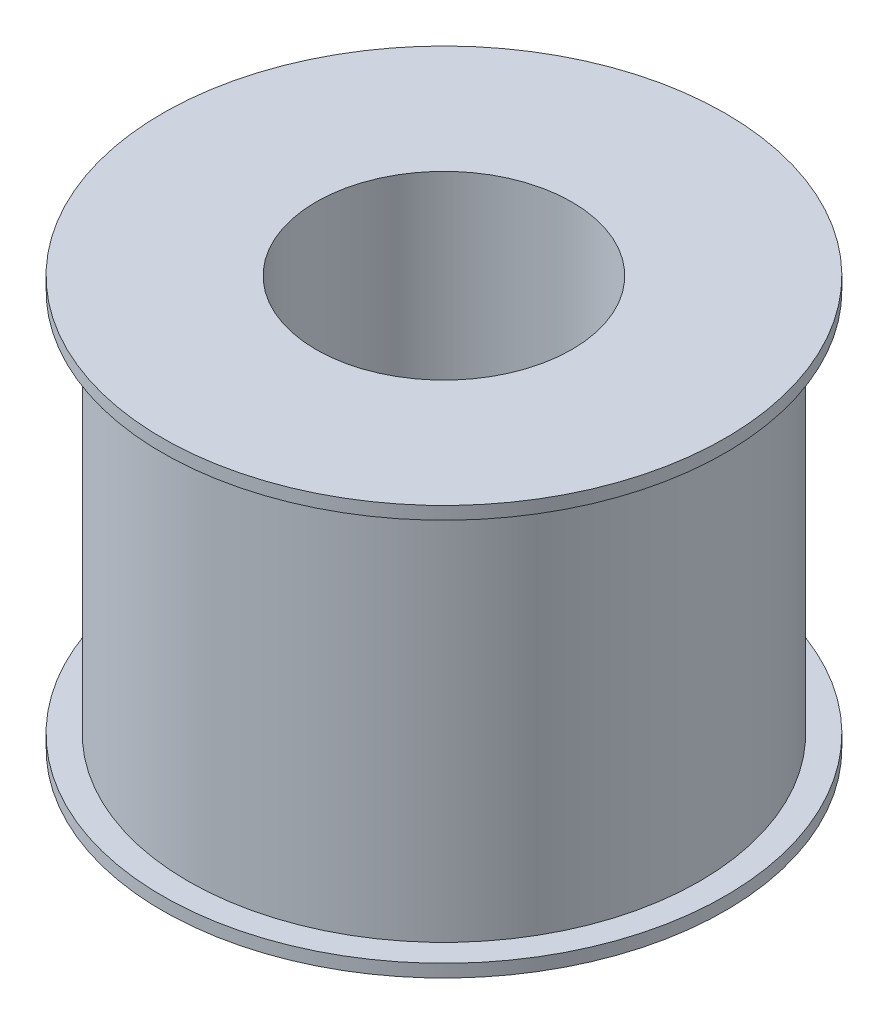
SolidWorks part; units mm, degrees
ref_plane "Front Plane" through (0, 0, 0) normal (0, 0, 1) x (1, 0, 0)
ref_plane "Top Plane" through (0, 0, 0) normal (0, 1, 0) x (1, 0, 0)
ref_plane "Right Plane" through (0, 0, 0) normal (1, 0, 0) x (0, 0, -1)
sketch "Sketch1" plane through (0, 0, 0) normal (0, 0, 1) x (1, 0, 0)
  line L0 (0, 0) -> (0, 9.1912) construction
  line L1 (5, 16.5441) -> (11, 16.5441)
  line L2 (11, 16.5441) -> (11, 16.0441)
  line L3 (11, 16.0441) -> (10, 16.0441)
  line L4 (10, 16.0441) -> (10, 1.0441)
  line L5 (10, 1.0441) -> (11, 1.0441)
  line L6 (11, 1.0441) -> (11, 0.5441)
  line L7 (11, 0.5441) -> (5, 0.5441)
  line L8 (5, 0.5441) -> (5, 16.5441)
  dimension "D1" = 0.5
  dimension "D2" = 1
  dimension "D3" = 15
  dimension "D4" = 10
  dimension "D5" = 20
revolve "Revolve1" add sketch "Sketch1" angle 360 about L0
